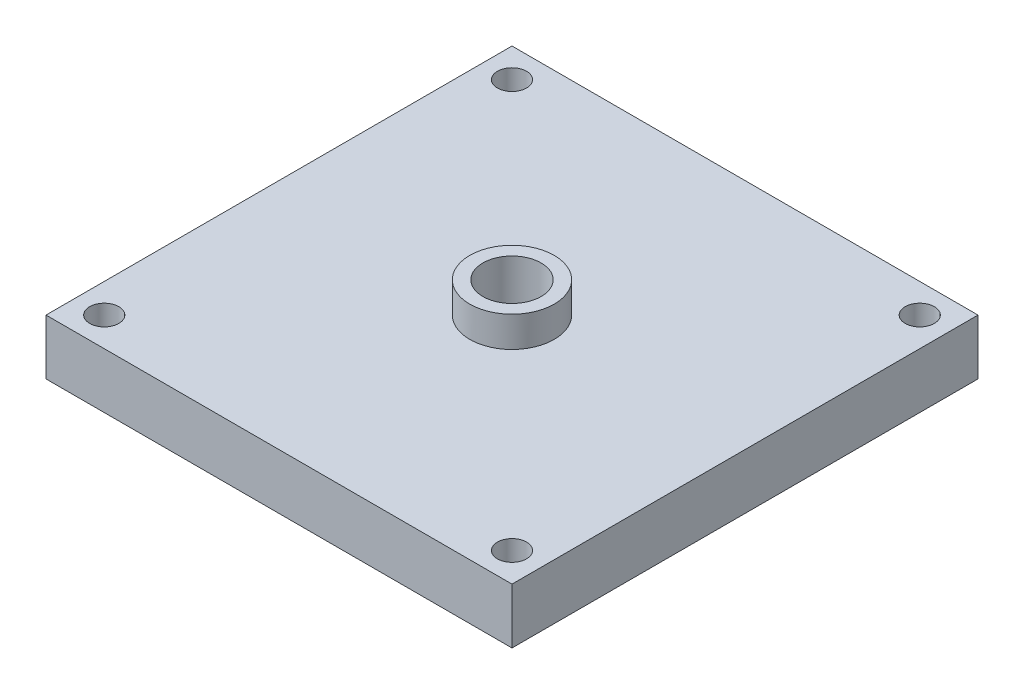
SolidWorks part; units mm, degrees
ref_plane "Front Plane" through (0, 0, 0) normal (0, 0, 1) x (1, 0, 0)
ref_plane "Top Plane" through (0, 0, 0) normal (0, 1, 0) x (1, 0, 0)
ref_plane "Right Plane" through (0, 0, 0) normal (1, 0, 0) x (0, 0, -1)
sketch "Sketch1" plane through (0, 0, 0) normal (0, 1, 0) x (1, 0, 0)
  line L1 (0, 0) -> (80, 0)
  line L2 (0, 0) -> (0, 80)
  line L3 (0, 80) -> (80, 80)
  line L4 (80, 0) -> (80, 80)
  circle A4 centre (5, 75) radius 2.5
  circle A5 centre (75, 75) radius 2.5
  circle A6 centre (75, 5) radius 2.5
  circle A7 centre (5, 5) radius 2.5
extrude "Boss-Extrude1" add sketch "Sketch1" along normal blind 9.5
sketch "Sketch3" plane through (0, 9.5, 0) normal (0, 1, 0) x (1, 0, 0)
  circle A0 centre (40, 40) radius 5
extrude "Cut-Extrude1" cut sketch "Sketch3" against normal mid plane 9.5
sketch "Sketch10" plane through (0, 4.75, 0) normal (0, 1, 0) x (1, 0, 0)
  circle A0 centre (40, 40) radius 5
  circle A1 centre (40, 40) radius 7.25
extrude "Boss-Extrude3" add sketch "Sketch10" along normal blind 10
